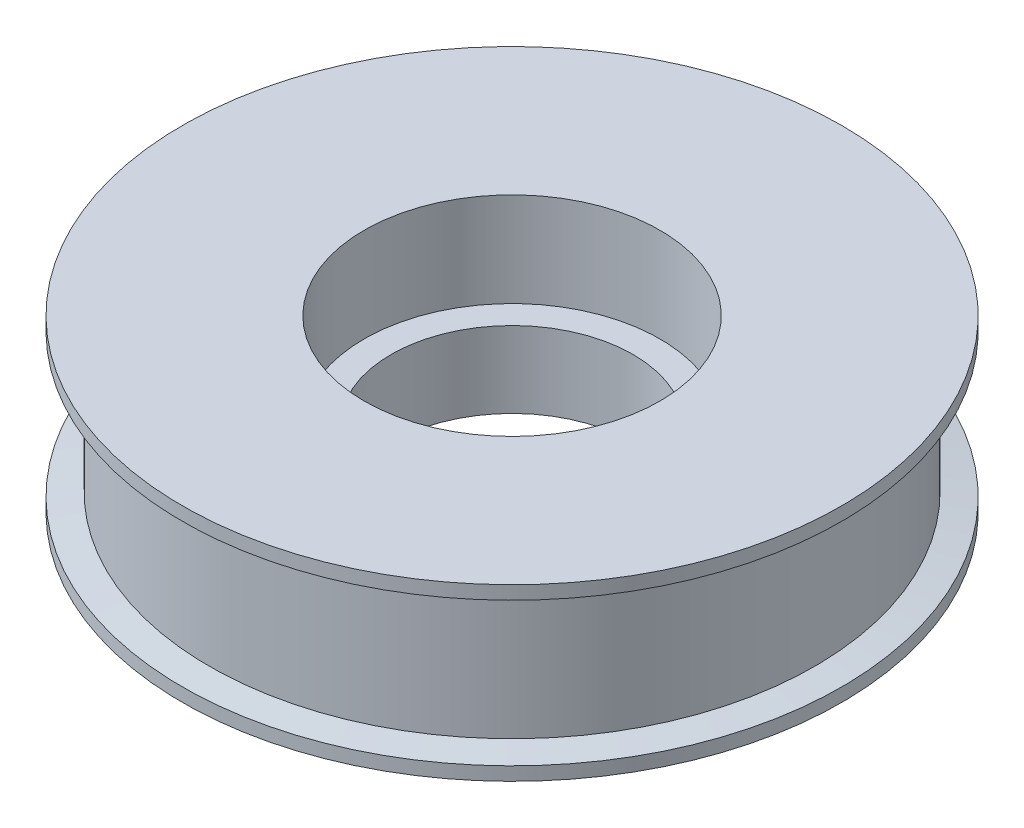
SolidWorks part; units mm, degrees
ref_plane "Front Plane" through (0, 0, 0) normal (0, 0, 1) x (1, 0, 0)
ref_plane "Top Plane" through (0, 0, 0) normal (0, 1, 0) x (1, 0, 0)
ref_plane "Right Plane" through (0, 0, 0) normal (1, 0, 0) x (0, 0, -1)
sketch "Sketch1" plane through (0, 0, 0) normal (0, 1, 0) x (1, 0, 0)
  circle A0 centre (0, 0) radius 11
  circle A1 centre (0, 0) radius 22.5
  dimension "D1" = 22
  dimension "D2" = 45
extrude "Boss-Extrude1" add sketch "Sketch1" along normal blind 11.66
sketch "Sketch2" plane through (0, 0, 0) normal (0, 0, 1) x (1, 0, 0)
  line L1 (22.5, 0) -> (22.5, 11.66) construction
  line L2 (22.5, 11.66) -> (24.5, 11.66)
  line L3 (22.5, 11.66) -> (22.5, 10.33)
  line L4 (22.5, 0.33) -> (24.5, 0)
  line L5 (24.5, 11.66) -> (24.5, 10.66)
  line L6 (22.5, 10.33) -> (24.5, 10.66)
  line L7 (22.5, -1) -> (24.5, -1)
  line L9 (0, 0) -> (0, 11.66) construction
  line L10 (24.5, -1) -> (24.5, 0)
  line L11 (11, 11.66) -> (-11, 11.66) construction
  line L13 (22.5, 0.33) -> (22.5, 4.66)
  line L14 (22.5, -1) -> (9, -1)
  line L15 (9, 0.33) -> (9, -1)
  line L16 (22.5, 4.66) -> (9, 4.66)
  line L17 (9, 0.33) -> (9, 4.66)
  dimension "D1" = 2
  dimension "D2" = 1.33
  dimension "D3" = 1.33
  dimension "D4" = 1
  dimension "D5" = 1
  dimension "D6" = 10
  dimension "D7" = 9
  dimension "D8" = 13.5
  dimension "D9" = 7
  dimension "D10" = 5.66
revolve "Revolve1" add sketch "Sketch2" angle 360 about L9
